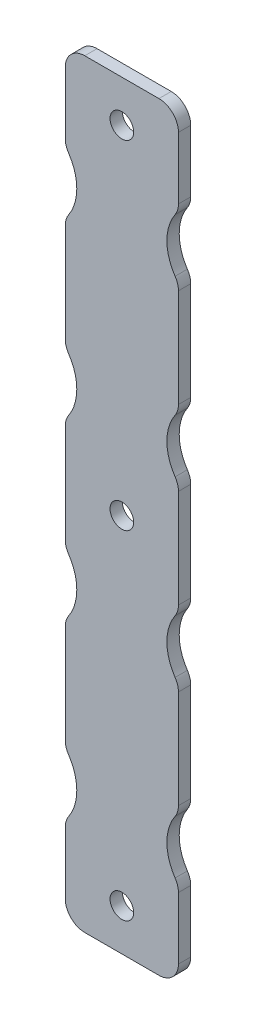
SolidWorks part; units mm, degrees
material "3003 Alloy"
ref_plane "X-Y Datum" through (0, 0, 0) normal (0, 0, 1) x (1, 0, 0)
ref_plane "X-Z Datum" through (0, 0, 0) normal (0, 1, 0) x (1, 0, 0)
ref_plane "Y-Z Datum" through (0, 0, 0) normal (1, 0, 0) x (0, 0, -1)
sketch "Sketch1" plane through (0, 0, 0) normal (0, 0, 1) x (1, 0, 0)
  line L0 (13.703, 64.5059) -> (16.8331, 64.5059) construction
  line L1 (7.903, 75.0059) -> (22.633, 75.0059) construction
  line L2 (7.903, 75.0059) -> (7.903, 68.5494)
  line L3 (7.903, -13.8121) -> (22.633, -13.8121) construction
  line L9 (22.633, 75.0059) -> (22.633, 68.5494)
  line L11 (15.268, 64.5059) -> (15.268, 75.0059) construction
  line L13 (7.903, 30.5969) -> (22.633, 30.5969) construction
  line L19 (7.903, 60.4624) -> (7.903, 45.9434)
  line L20 (7.903, 37.8564) -> (7.903, 23.3374)
  line L21 (7.903, 15.2504) -> (7.903, 0.7314)
  line L22 (7.903, -7.3556) -> (7.903, -13.8121)
  line L23 (22.633, -7.3556) -> (22.633, -13.8121)
  line L24 (22.633, 15.2504) -> (22.633, 0.7314)
  line L25 (22.633, 37.8564) -> (22.633, 23.3374)
  line L26 (22.633, 60.4624) -> (22.633, 45.9434)
  line L27 (15.268, 78.736) -> (15.268, 80.006) construction
  line L28 (7.903, 75.0059) -> (7.903, 80.006)
  line L29 (7.903, 80.006) -> (22.633, 80.006)
  line L30 (22.633, 80.006) -> (22.633, 75.0059)
  line L31 (22.633, -18.8123) -> (22.633, -13.8121)
  line L32 (7.903, -18.8123) -> (22.633, -18.8123)
  line L33 (7.903, -13.8121) -> (7.903, -18.8123)
  circle A4 centre (3.203, -3.3121) radius 4.7 construction
  arc A5 (7.903, -7.3556) -> (7.903, 0.7314) centre (3.203, -3.3121) ccw
  circle A14 centre (15.268, 74.5831) radius 2.5146 construction
  circle A15 centre (15.268, 74.5831) radius 1.5367
  circle A16 centre (15.268, -13.3894) radius 1.5367
  circle A17 centre (15.268, -13.3894) radius 2.5146 construction
  arc A18 (7.903, 15.2504) -> (7.903, 23.3374) centre (3.203, 19.2939) ccw
  arc A19 (7.903, 37.8564) -> (7.903, 45.9434) centre (3.203, 41.8999) ccw
  arc A20 (7.903, 60.4624) -> (7.903, 68.5494) centre (3.203, 64.5059) ccw
  arc A21 (22.633, -7.3556) -> (22.633, 0.7314) centre (27.333, -3.3121) cw
  arc A22 (22.633, 15.2504) -> (22.633, 23.3374) centre (27.333, 19.2939) cw
  arc A23 (22.633, 37.8564) -> (22.633, 45.9434) centre (27.333, 41.8999) cw
  arc A24 (22.633, 60.4624) -> (22.633, 68.5494) centre (27.333, 64.5059) cw
  circle A25 centre (15.268, 74.5831) radius 4.1529 construction
  dimension "D1" = 4
  dimension "D2" = 10.0772
  dimension "D3" = 88.818
extrude "Boss-Extrude1" add sketch "Sketch1" along normal blind 1.6
fillet "Fillet1" radius 2.54 20 edges at (7.903, 60.4624, 0.8) (7.903, 68.5494, 0.8) (7.903, 45.9434, 0.8) (7.903, 37.8564, 0.8) (7.903, 23.3374, 0.8) (7.903, 15.2504, 0.8) (7.903, 0.7314, 0.8) (7.903, -7.3556, 0.8) (22.633, 0.7314, 0.8) (22.633, -7.3556, 0.8) (22.633, 15.2504, 0.8) (22.633, 23.3374, 0.8) (22.633, 45.9434, 0.8) (22.633, 37.8564, 0.8) (22.633, 68.5494, 0.8) (22.633, 60.4624, 0.8) (7.903, 80.006, 0.8) (22.633, 80.006, 0.8) (22.633, -18.8123, 0.8) (7.903, -18.8123, 0.8)
sketch "Sketch2" plane through (0, 0, 1.6) normal (0, 0, 1) x (1, 0, 0)
  line L1 (7.903, 75.0059) -> (22.633, 75.0059)
  line L2 (7.903, 75.0059) -> (7.903, -13.8121)
  line L3 (7.903, -13.8121) -> (22.633, -13.8121)
  line L4 (22.633, 75.0059) -> (22.633, -13.8121)
sketch "Sketch3" plane through (0, 0, 1.6) normal (0, 0, 1) x (1, 0, 0)
  line L0 (15.268, 75.0059) -> (15.268, -13.8121) construction
  circle A0 centre (15.268, 30.5969) radius 1.5367
extrude "Cut-Extrude1" cut sketch "Sketch3" against normal through all
sketch "Sketch5" plane through (0, 0, 1.6) normal (0, 0, 1) x (1, 0, 0)
  line L0 (15.268, 74.5831) -> (15.268, 72.7931)
  circle A0 centre (15.268, 76.9581) radius 4.165
